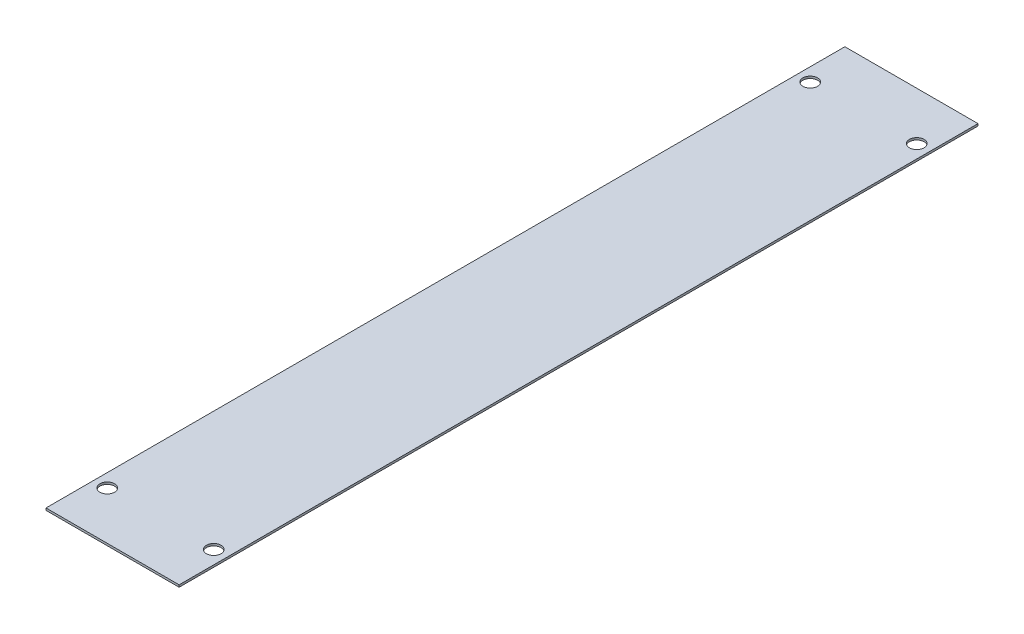
SolidWorks part; units mm, degrees
ref_plane "Front Plane" through (0, 0, 0) normal (0, 0, 1) x (1, 0, 0)
ref_plane "Top Plane" through (0, 0, 0) normal (0, 1, 0) x (1, 0, 0)
ref_plane "Right Plane" through (0, 0, 0) normal (1, 0, 0) x (0, 0, -1)
sketch "Sketch1" plane through (0, 0, 0) normal (0, 1, 0) x (1, 0, 0)
  line L1 (12.5, -75) -> (-12.5, -75)
  line L2 (12.5, -75) -> (12.5, 75)
  line L3 (12.5, 75) -> (-12.5, 75)
  line L4 (-12.5, -75) -> (-12.5, 75)
  line L5 (12.5, -75) -> (-12.5, 75) construction
  line L6 (12.5, 75) -> (-12.5, -75) construction
  point P0 (0, 0)
  dimension "D1" = 25
  dimension "D2" = 150
extrude "Boss-Extrude1" add sketch "Sketch1" along normal blind 0.4
sketch "Sketch2" plane through (0, 0.4, 0) normal (0, 1, 0) x (1, 0, 0)
  line L0 (0, -1000) -> (0, 49000) construction
  line L1 (-1000, 0) -> (49000, 0) construction
  circle A0 centre (-10, 66) radius 1.38
  dimension "D2" = 66
  dimension "D3" = 2.76
  dimension "D1" = 10
extrude "Cut-Extrude1" cut sketch "Sketch2" against normal blind 0.4
mirror "Mirror1" about plane through (0, 0, 0) normal (1, 0, 0) of "Cut-Extrude1"
mirror "Mirror2" about plane through (0, 0, 0) normal (0, 0, 1) of "Cut-Extrude1", "Mirror1"
